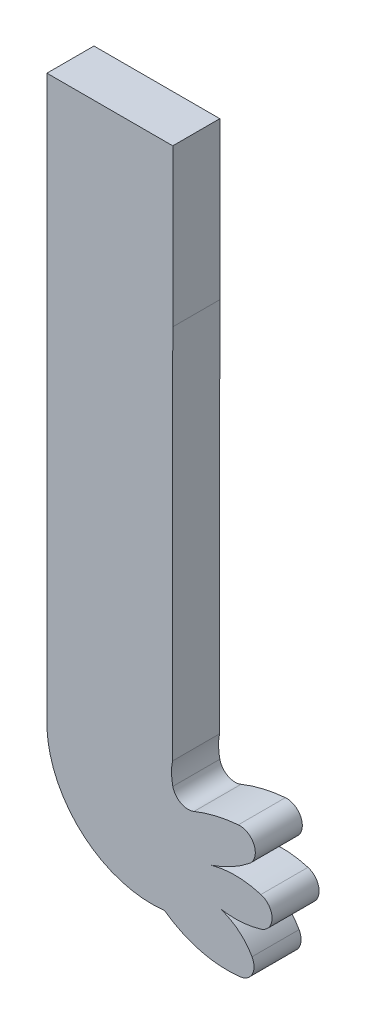
SolidWorks part; units mm, degrees
ref_plane "Alzado" through (0, 0, 0) normal (0, 0, 1) x (1, 0, 0)
ref_plane "Planta" through (0, 0, 0) normal (0, 1, 0) x (1, 0, 0)
ref_plane "Vista lateral" through (0, 0, 0) normal (1, 0, 0) x (0, 0, -1)
sketch "Model" plane through (0, 0, 0) normal (0, 0, 1) x (1, 0, 0)
  line L0 (27.4679, 39.6803) -> (27.4679, 22.0971)
  line L1 (35.494, 39.6803) -> (27.4679, 39.6803)
  line L2 (35.494, 29.6803) -> (35.494, 39.6803)
  line L3 (35.4761, 5.6935) -> (35.494, 29.6803)
  line L4 (27.4679, 3.5138) -> (27.4679, 22.0971)
  arc A0 (27.4679, 3.5138) -> (34.9679, -2.8197) centre (34.1485, 3.8174) ccw
  arc A1 (34.9679, -2.8197) -> (39.8004, -4.0692) centre (38.9679, 2.6803) ccw
  arc A2 (39.8004, -4.0692) -> (40.5496, -2.5866) centre (39.678, -3.0768) ccw
  arc A3 (40.5496, -2.5866) -> (38.4974, -0.9373) centre (37.4679, -4.3197) ccw
  arc A4 (38.4974, -0.9373) -> (41.1166, -0.7769) centre (39.4679, 4.6803) ccw
  arc A5 (41.1166, -0.7769) -> (41.1166, 1.1376) centre (40.8274, 0.1803) ccw
  arc A6 (41.1166, 1.1376) -> (37.9679, 1.1803) centre (39.4679, -4.3197) ccw
  arc A7 (37.9679, 1.1803) -> (40.379, 2.4851) centre (35.4679, 8.6803) ccw
  arc A8 (40.379, 2.4851) -> (39.6754, 4.2653) centre (39.7578, 3.2687) ccw
  arc A9 (39.6754, 4.2653) -> (36.8493, 3.5913) centre (40.4679, -5.3197) ccw
  arc A10 (35.4972, 4.2996) -> (36.8493, 3.5913) centre (36.4731, 4.5179) ccw
  arc A11 (35.4761, 5.6935) -> (35.4972, 4.2996) centre (38.8414, 5.0475) ccw
extrude "Saliente-Extruir1" add sketch "Model" along normal blind 3
